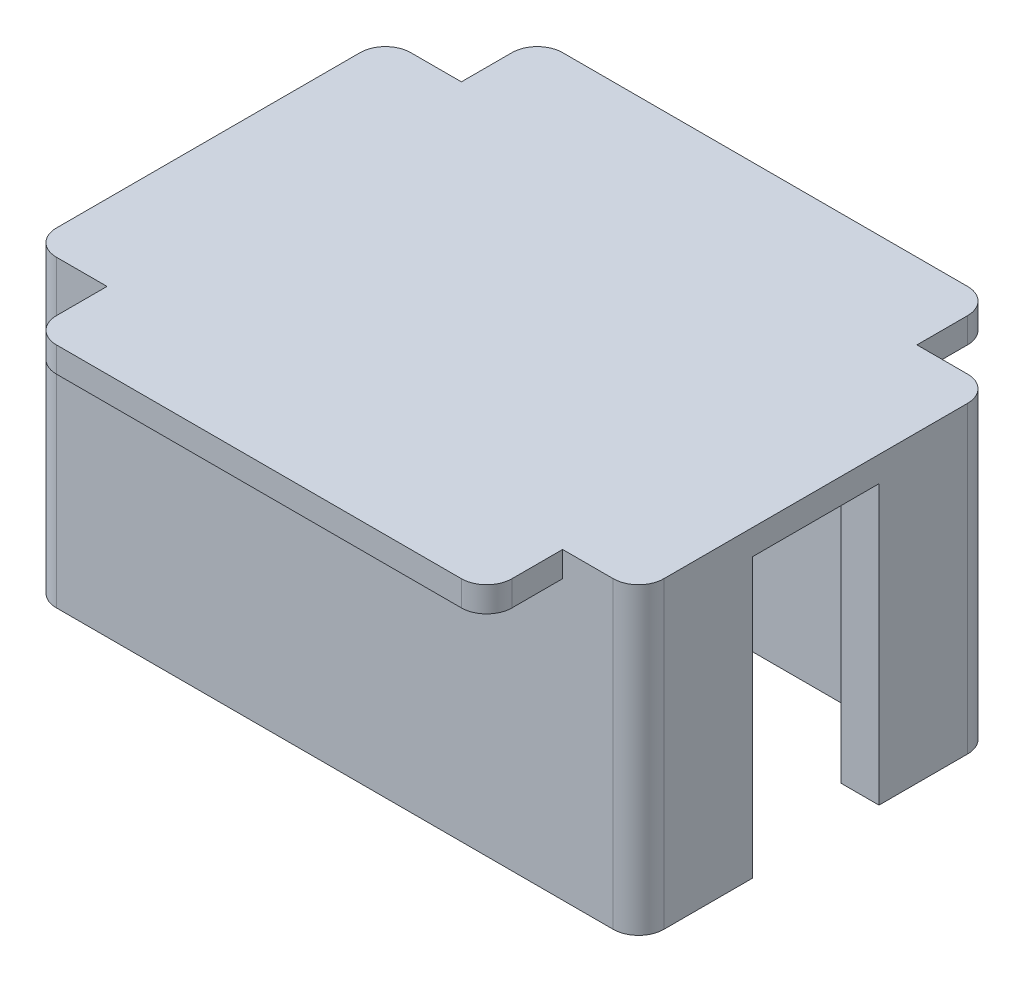
SolidWorks part; units mm, degrees
ref_plane "Front Plane" through (0, 0, 0) normal (0, 0, 1) x (1, 0, 0)
ref_plane "Top Plane" through (0, 0, 0) normal (0, 1, 0) x (1, 0, 0)
ref_plane "Right Plane" through (0, 0, 0) normal (1, 0, 0) x (0, 0, -1)
sketch "Sketch6" plane through (0, 0, 0) normal (0, 1, 0) x (-1, 0, 0)
  line L1 (-27.5, 11.5) -> (20.5, 11.5)
  line L2 (-27.5, 11.5) -> (-27.5, -16.5)
  line L3 (-27.5, -16.5) -> (20.5, -16.5)
  line L4 (20.5, 11.5) -> (20.5, -16.5)
  line L7 (-24.5, 8) -> (17.5, 8)
  line L8 (-24.5, 8) -> (-24.5, -13)
  line L9 (-24.5, -13) -> (17.5, -13)
  line L10 (17.5, 8) -> (17.5, -13)
  dimension "D1" = 28
  dimension "D2" = 48
  dimension "D3" = 42
  dimension "D4" = 21
  dimension "D5" = 3
  dimension "D6" = 3.5
extrude "Boss-Extrude20" add sketch "Sketch6" against normal blind 22 separate body
sketch "Sketch9" plane through (0, 0, 0) normal (0, 1, 0) x (-1, 0, 0)
  line L1 (-27.5, 11.5) -> (20.5, 11.5)
  line L2 (-27.5, 11.5) -> (-27.5, -16.5)
  line L3 (-27.5, -16.5) -> (20.5, -16.5)
  line L4 (20.5, 11.5) -> (20.5, -16.5)
extrude "Boss-Extrude22" add sketch "Sketch9" along normal blind 2
fillet "Fillet1" radius 2 4 edges at (-20.5, -10, -16.5) (27.5, -10, -16.5) (-20.5, -10, 11.5) (27.5, -10, 11.5)
sketch "Sketch11" plane through (0, 2, 0) normal (0, 1, 0) x (1, 0, 0)
  line L0 (25.5, 16.5) -> (-18.5, 16.5) construction
  line L6 (-14.5, 16.5) -> (21.5, 16.5)
  line L7 (-14.5, 16.5) -> (-14.5, 22.5)
  line L8 (-14.5, 22.5) -> (21.5, 22.5)
  line L9 (21.5, 16.5) -> (21.5, 22.5)
  line L10 (-20.5, 14.5) -> (-20.5, -9.5) construction
  line L11 (27.5, -9.5) -> (27.5, 14.5) construction
  line L12 (-20.5, 2.5) -> (27.5, 2.5) construction
  line L13 (21.5, -11.5) -> (21.5, -17.5)
  line L14 (-14.5, -17.5) -> (21.5, -17.5)
  line L15 (-14.5, -11.5) -> (-14.5, -17.5)
  line L16 (-14.5, -11.5) -> (21.5, -11.5)
  dimension "D1" = 6
  dimension "6" = 6
  dimension "D3" = 6
extrude "Boss-Extrude23" add sketch "Sketch11" against normal blind 2
fillet "Fillet2" radius 2 4 edges at (21.5, 1, 17.5) (21.5, 1, -22.5) (-14.5, 1, -22.5) (-14.5, 1, 17.5)
sketch "Sketch12" plane through (0, -22, 0) normal (0, -1, 0) x (1, 0, 0)
  line L0 (24.5, 2.5) -> (27.5, 2.5)
  line L1 (24.5, 8) -> (24.5, -13) construction
  line L2 (27.5, 9.5) -> (27.5, -14.5) construction
  line L3 (27.5, 2.5) -> (27.5, -7.5)
  line L4 (27.5, -7.5) -> (24.5, -7.5)
  line L5 (24.5, -7.5) -> (24.5, 2.5)
  line L6 (-18.5, 11.5) -> (25.5, 11.5) construction
  line L7 (25.5, -16.5) -> (-18.5, -16.5) construction
  dimension "D1" = 9
  dimension "D2" = 9
extrude "Cut-Extrude2" cut sketch "Sketch12" against normal up to surface (22 mm away) up to face at (3.5, 0, -2.5)
